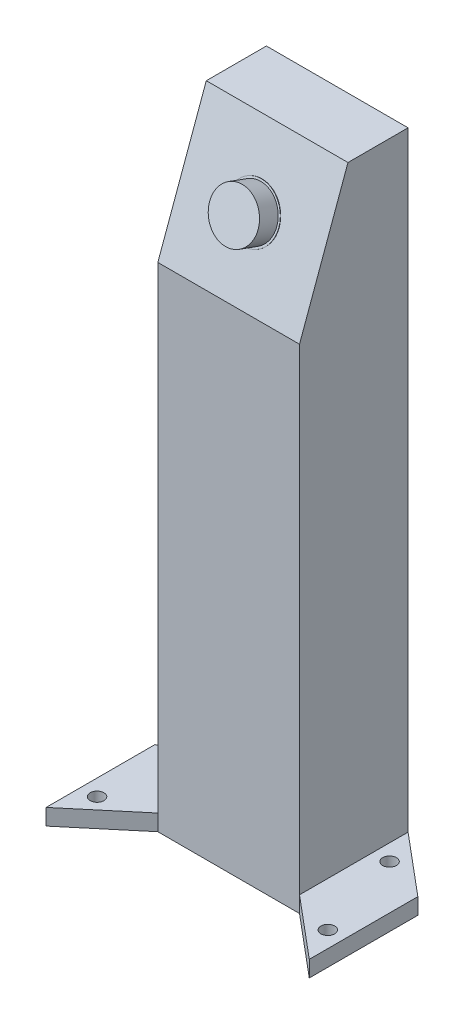
SolidWorks part; units mm, degrees
ref_plane "Ebene vorne" through (0, 0, 0) normal (0, 0, 1) x (1, 0, 0)
ref_plane "Ebene oben" through (0, 0, 0) normal (0, 1, 0) x (1, 0, 0)
ref_plane "Ebene rechts" through (0, 0, 0) normal (1, 0, 0) x (0, 0, -1)
sketch "Skizze1" plane through (0, 0, 0) normal (1, 0, 0) x (0, 0, -1)
  line L0 (0, 0) -> (11.9707, 0)
  line L1 (0, 0) -> (0, 121.8)
  line L2 (0, 121.8) -> (11.9707, 154.6892)
  line L3 (11.9707, 154.6892) -> (11.9707, 0) construction
  line L4 (11.9707, 0) -> (26.82, 0)
  line L5 (26.82, 0) -> (26.82, 154.6892)
  line L6 (26.82, 154.6892) -> (11.9707, 154.6892)
  dimension "D1" = 70
  dimension "D2" = 121.8
  dimension "D3" = 35
  dimension "D4" = 26.82
extrude "Aufsatz-Linear austragen1" add sketch "Skizze1" along normal blind 35
sketch "Skizze3" plane through (0, 14.2479, 39.1458) normal (0, 0.342, 0.9397) x (1, 0, 0)
  line L0 (0, 149.4546) -> (35, 114.4546) construction
  line L1 (17.5, 131.9546) -> (35, 149.4546) construction
  line L2 (35, 149.4546) -> (0, 149.4546) construction
  line L3 (35, 149.4546) -> (35, 114.4546) construction
  circle A0 centre (17.5, 131.9546) radius 6
  dimension "D1" = 12
extrude "Aufsatz-Linear austragen2" add sketch "Skizze3" along normal blind 5
sketch "Skizze4" plane through (0, 14.2479, 39.1458) normal (0, 0.342, 0.9397) x (1, 0, 0)
  circle A0 centre (17.5, 131.9546) radius 6.5
  dimension "D1" = 13
extrude "Aufsatz-Linear austragen3" add sketch "Skizze4" along normal blind 0.1
ref_plane "Ebene1" through (0, 121.8, 0) normal (0, -1, 0) x (-1, 0, 0)
ref_plane "Ebene2" [suppressed] through (0, 4.5, 0) normal (0, 1, 0) x (1, 0, 0)
sketch "Skizze7" [suppressed] plane through (0, 4.5, 0) normal (0, -1, 0) x (-1, 0, 0)
  line L0 (-35, 26.82) -> (0, 26.82) construction
  line L1 (-35, 0) -> (0, 26.82) construction
  line L2 (-17.5, 13.41) -> (-17.5, 26.82) construction
  line L4 (-17.5, 13.41) -> (-35, 13.41) construction
  line L5 (-35, 0) -> (-35, 26.82) construction
  circle A0 centre (-28.5, 5) radius 3
  circle A1 centre (-6.5, 5) radius 3
  circle A2 centre (-6.5, 21.82) radius 3
  circle A3 centre (-28.5, 21.82) radius 3
  dimension "D1" = 6
  dimension "D2" = 11
  dimension "D3" = 5
extrude "Schnitt-Linear austragen1" [suppressed] cut sketch "Skizze7" against normal through all
hole_wizard "Ø3.6 (3.6) Durchmesser Bohrung1" [suppressed] positions "3D-Skizze3" profile "Skizze8" hole size "Ø3.6" standard "DIN"
sketch3d "3D-Skizze3" [suppressed]
  line L0 (6.5, 152.4798, -5) -> (6.5, 4.5, -5) construction
  line L1 (6.5, 163.3892, -21.82) -> (6.5, 4.5, -21.82) construction
  line L2 (28.5, 163.3892, -21.82) -> (28.5, 4.5, -21.82) construction
  line L3 (28.5, 152.4798, -5) -> (28.5, 4.5, -5) construction
  point P0 (6.5, 4.5, -5)
  point P4 (6.5, 4.5, -21.82)
  point P8 (28.5, 4.5, -21.82)
  point P12 (28.5, 4.5, -5)
sketch "Skizze8" [suppressed] plane through (6.5, 4.5, -5) normal (1, 0, 0) x (0, 0, 1)
  line L0 (0, 0) -> (0, 4.5)
  line L1 (0, 4.5) -> (1.8, 4.5)
  line L2 (1.8, 4.5) -> (1.8, 0)
  line L5 (1.8, 0) -> (0, 0)
  line L11 (0, -6.35) -> (0, 107.95) construction
  dimension "Bohrerdurchmesser" = 3.6
  dimension "Bohrungstiefe" = 4.5
sketch "Skizze9" plane through (0, 0, 0) normal (0, -1, 0) x (1, 0, 0)
  line L0 (35, -26.82) -> (50, -14.2335)
  line L1 (50, -14.2335) -> (50, 12.5865)
  line L2 (50, 12.5865) -> (35, 0)
  line L3 (35, -26.82) -> (0, -26.82) construction
  line L4 (35, 0) -> (35, -26.82) construction
  line L5 (35, 0) -> (35, -26.82)
  line L6 (17.5, -26.82) -> (17.5, -16.0755) construction
  line L7 (0, 0) -> (0, -26.82)
  line L8 (-15, 12.5865) -> (0, 0)
  line L9 (-15, -14.2335) -> (-15, 12.5865)
  line L10 (0, -26.82) -> (-15, -14.2335)
  line L11 (46, 4.0085) -> (50, 4.0085) construction
  line L12 (46, 4.0085) -> (43.4288, 7.0726) construction
  line L13 (39, -18.242) -> (41.5712, -21.3062) construction
  line L14 (39, -18.242) -> (35, -18.242) construction
  circle A0 centre (46, 4.0085) radius 1.7
  circle A1 centre (39, -18.242) radius 1.7
  circle A3 centre (-4, -18.242) radius 1.7
  circle A4 centre (-11, 4.0085) radius 1.7
  dimension "D3" = 3.4
  dimension "D1" = 140
  dimension "D2" = 15
  dimension "D4" = 4
  dimension "D5" = 4
extrude "Aufsatz-Linear austragen4" add sketch "Skizze9" against normal blind 4
